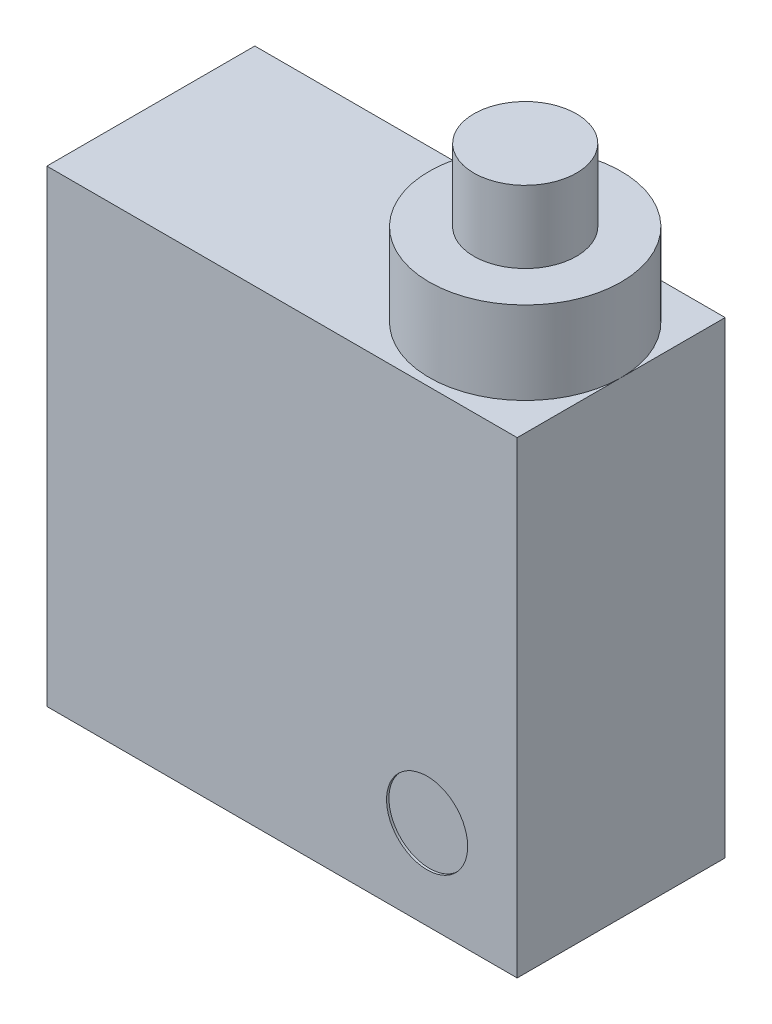
SolidWorks part; units mm, degrees
ref_plane "Front Plane" through (0, 0, 0) normal (0, 0, 1) x (1, 0, 0)
ref_plane "Top Plane" through (0, 0, 0) normal (0, 1, 0) x (1, 0, 0)
ref_plane "Right Plane" through (0, 0, 0) normal (1, 0, 0) x (0, 0, -1)
sketch "Sketch1" plane through (0, 0, 0) normal (0, 1, 0) x (1, 0, 0)
  line L1 (0, 0) -> (19.9, 0)
  line L2 (0, 0) -> (0, 8.8)
  line L3 (0, 8.8) -> (19.9, 8.8)
  line L4 (19.9, 0) -> (19.9, 8.8)
  line L5 (0, 0) -> (19.9, 8.8) construction
  line L6 (0, 8.8) -> (19.9, 0) construction
  point P4 (9.95, 4.4)
extrude "Boss-Extrude1" add sketch "Sketch1" along normal blind 19.8 contours L3 L4 L1 L2
sketch "Sketch2" plane through (0, 19.8, 0) normal (0, 1, 0) x (1, 0, 0)
  circle A0 centre (15.8393, 4.4) radius 2.1721
extrude "Boss-Extrude2" add sketch "Sketch2" along normal blind 6.55
sketch "Sketch3" plane through (0, 19.8, 0) normal (0, 1, 0) x (1, 0, 0)
  circle A0 centre (15.8393, 4.4) radius 4.0607
extrude "Boss-Extrude3" add sketch "Sketch3" along normal blind 3.5
sketch "Sketch4" plane through (0, 0, 0) normal (0, 0, 1) x (1, 0, 0)
  circle A0 centre (16.0894, 3.774) radius 1.716
extrude "Cut-Extrude1" cut sketch "Sketch4" against normal blind 0.1
